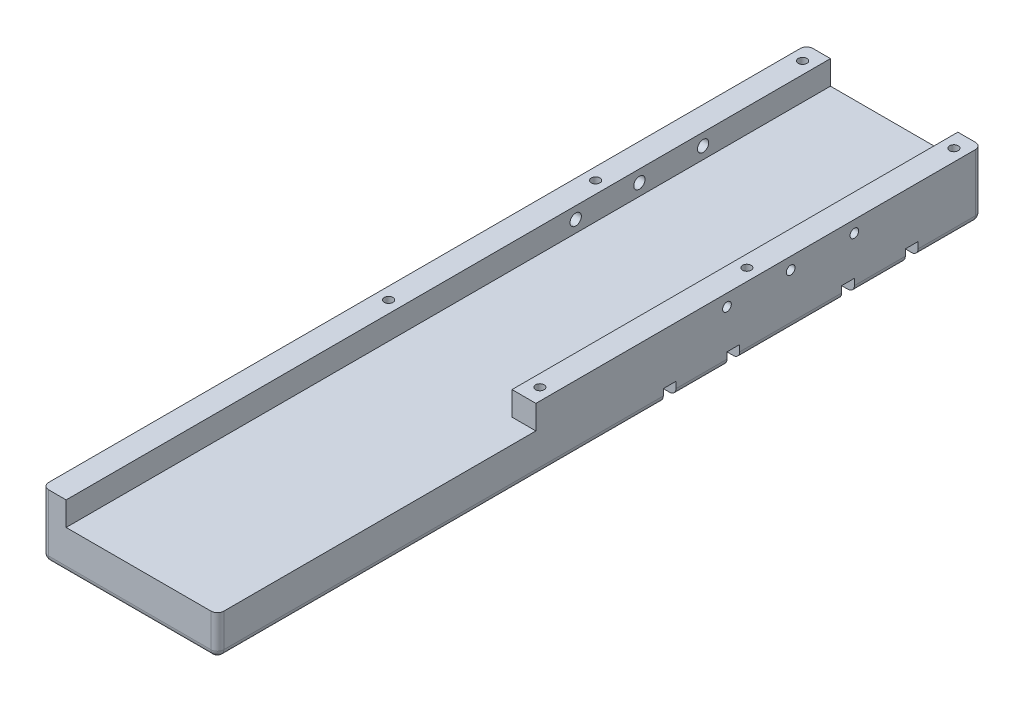
SolidWorks part; units mm, degrees
ref_plane "Front Plane" through (0, 0, 0) normal (0, 0, 1) x (1, 0, 0)
ref_plane "Top Plane" through (0, 0, 0) normal (0, 1, 0) x (1, 0, 0)
ref_plane "Right Plane" through (0, 0, 0) normal (1, 0, 0) x (0, 0, -1)
sketch "Sketch1" plane through (0, 0, 0) normal (0, 1, 0) x (1, 0, 0)
  line L1 (0, 0) -> (69.85, 0)
  line L2 (0, 0) -> (0, 304.8)
  line L3 (0, 304.8) -> (69.85, 304.8)
  line L4 (69.85, 0) -> (69.85, 304.8)
  dimension "D1" = 69.85
  dimension "D2" = 304.8
extrude "Boss-Extrude1" add sketch "Sketch1" along normal blind 25.4
fillet "Fillet1" radius 2.54 8 edges at (69.85, 12.7, -304.8) (0, 12.7, -304.8) (34.925, 0, -304.8) (0, 12.7, 0) (69.85, 12.7, 0) (34.925, 0, 0) (69.85, 0, -152.4) (0, 0, -152.4)
sketch "Sketch2" plane through (0, 0, 0) normal (0, -1, 0) x (1, 0, 0)
  line L0 (69.85, 0) -> (69.85, -304.8) construction
  line L1 (69.85, -177.8) -> (0, -177.8)
  line L2 (69.85, -177.8) -> (69.85, -182.88)
  line L3 (69.85, -182.88) -> (0, -182.88)
  line L4 (0, -177.8) -> (0, -182.88)
  line L5 (0, -304.8) -> (0, 0) construction
  line L7 (69.85, -203.2) -> (0, -203.2)
  line L8 (69.85, -203.2) -> (69.85, -208.28)
  line L9 (69.85, -208.28) -> (0, -208.28)
  line L10 (0, -203.2) -> (0, -208.28)
  line L11 (69.85, -248.92) -> (0, -248.92)
  line L12 (69.85, -248.92) -> (69.85, -254)
  line L13 (69.85, -254) -> (0, -254)
  line L14 (0, -248.92) -> (0, -254)
  line L15 (69.85, -274.32) -> (0, -274.32)
  line L16 (69.85, -274.32) -> (69.85, -279.4)
  line L17 (69.85, -279.4) -> (0, -279.4)
  line L18 (0, -274.32) -> (0, -279.4)
  line L19 (69.85, -304.8) -> (0, -304.8) construction
  dimension "D1" = 5.08
  dimension "D2" = 25.4
  dimension "D3" = 45.72
  dimension "D5" = 25.4
  dimension "D4" = 2
extrude "Cut-Extrude1" cut sketch "Sketch2" against normal blind 5.08
sketch "Sketch3" plane through (0, 25.4, 0) normal (0, 1, 0) x (1, 0, 0)
  line L0 (67.31, 304.8) -> (2.54, 304.8) construction
  line L1 (9.525, 304.8) -> (60.325, 304.8)
  line L2 (9.525, 304.8) -> (9.525, 0)
  line L3 (9.525, 0) -> (60.325, 0)
  line L4 (60.325, 304.8) -> (60.325, 0)
  line L5 (2.54, 0) -> (67.31, 0) construction
  line L6 (0, 302.26) -> (0, 2.54) construction
  line L7 (69.85, 2.54) -> (69.85, 302.26) construction
  dimension "D1" = 9.525
  dimension "D2" = 9.525
extrude "Cut-Extrude2" cut sketch "Sketch3" against normal blind 9.525
sketch "Sketch4" plane through (0, 0, 0) normal (-1, 0, 0) x (0, 0, 1)
  line L0 (-304.8, 20.6375) -> (0, 20.6375) construction
  line L1 (-304.8, 2.54) -> (-304.8, 25.4) construction
  line L3 (-302.26, 25.4) -> (-2.54, 25.4) construction
  line L4 (0, 25.4) -> (0, 2.54) construction
  circle A0 centre (-203.2, 20.6375) radius 2.2479
  circle A1 centre (-228.6, 20.6375) radius 2.2479
  circle A2 centre (-254, 20.6375) radius 2.2479
  dimension "D2" = 50.8
  dimension "D3" = 25.4
  dimension "D4" = 25.4
  dimension "D5" = 4.4958
  dimension "D1" = 4.7625
extrude "Cut-Extrude3" cut sketch "Sketch4" against normal up to next
hole_wizard "#8-32 Tapped Hole1" positions "Sketch10" profile "Sketch11" tap size "#8-32" standard "ANSI Inch"
sketch "Sketch10" plane through (0, 25.4, 0) normal (0, 1, 0) x (1, 0, 0)
  line L0 (67.31, 304.8) -> (60.325, 304.8) construction
  line L1 (69.85, 2.54) -> (69.85, 302.26) construction
  line L3 (69.85, 215.9) -> (-11.011, 215.9) construction
  line L5 (0, 302.26) -> (0, 2.54) construction
  point P0 (65.0875, 298.45)
  point P3 (4.7625, 298.45)
  point P6 (65.0875, 215.9)
  point P9 (4.7625, 215.9)
  point P44 (65.0875, 133.35)
  point P45 (4.7625, 133.35)
  point P47 (4.7625, 215.9)
  dimension "D1" = 6.35
  dimension "D2" = 4.7625
  dimension "D3" = 82.55
  dimension "D4" = 4.7625
sketch "Sketch11" plane through (65.0875, 25.4, -298.45) normal (1, 0, 0) x (0, 0, 1)
  line L0 (0, 0) -> (0, 11.7058)
  line L1 (0, 11.7058) -> (1.7272, 10.668)
  line L2 (1.7272, 10.668) -> (1.7272, 0)
  line L5 (1.7272, 0) -> (0, 0)
  line L10 (0, 11.7058) -> (-1.7272, 10.668) construction
  line L11 (0, -6.35) -> (0, 107.95) construction
  dimension "Tap Drill Dia." = 3.4544
  dimension "Tap Drill Depth" = 10.668
  dimension "Drill Angle" = 118
cosmetic thread "Hole Thread1" parameters "D1"=8.382, "D2"=4.1656
cosmetic thread "Hole Thread2" parameters "D1"=8.382, "D2"=4.1656
cosmetic thread "Hole Thread3" parameters "D1"=8.382, "D2"=4.1656
cosmetic thread "Hole Thread4" parameters "D1"=8.382, "D2"=4.1656
cosmetic thread "Hole Thread7" parameters "D1"=8.382, "D2"=4.1656
cosmetic thread "Hole Thread8" parameters "D1"=8.382, "D2"=4.1656
cosmetic thread "Hole Thread25" parameters "D1"=8.382, "D2"=4.1656
hole_wizard "#8-32 Tapped Hole2" positions "Sketch12" profile "Sketch13" tap size "#8-32" standard "ANSI Inch" end condition up to next
sketch "Sketch12" plane through (69.85, 0, 0) normal (1, 0, 0) x (0, 0, -1)
  line L0 (2.54, 25.4) -> (302.26, 25.4) construction
  line L2 (304.8, 25.4) -> (304.8, 2.54) construction
  point P0 (203.2, 20.6375)
  point P2 (228.6, 20.6375)
  point P4 (254, 20.6375)
  dimension "D1" = 4.7625
  dimension "D2" = 25.4
  dimension "D3" = 25.4
  dimension "D4" = 50.8
sketch "Sketch13" plane through (69.85, 20.6375, -203.2) normal (0, 1, 0) x (0, 0, -1)
  line L0 (0, 0) -> (0, 9.525)
  line L1 (0, 9.525) -> (1.7272, 9.525)
  line L2 (1.7272, 9.525) -> (1.7272, 0)
  line L5 (1.7272, 0) -> (0, 0)
  line L11 (0, -6.35) -> (0, 107.95) construction
  dimension "Thru Tap Drill Dia." = 3.4544
  dimension "Thru Tap Drill Depth" = 9.525
cosmetic thread "Hole Thread9" parameters "D2"=4.1656
cosmetic thread "Hole Thread10" parameters "D2"=4.1656
cosmetic thread "Hole Thread11" parameters "D2"=4.1656
hole_wizard "#8-32 Tapped Hole3" positions "Sketch14" profile "Sketch15" tap size "#8-32" standard "ANSI Inch"
sketch "Sketch14" plane through (0, 0, 0) normal (0, -1, 0) x (-1, 0, 0)
  line L0 (0, 302.26) -> (0, 279.4) construction
  line L1 (-69.85, 279.4) -> (-69.85, 302.26) construction
  line L2 (-2.54, 264.16) -> (-65.2153, 264.16) construction
  line L3 (-2.54, 254) -> (-2.54, 274.32) construction
  line L5 (-2.54, 193.04) -> (-66.4882, 193.04) construction
  line L6 (-2.54, 182.88) -> (-2.54, 203.2) construction
  line L8 (-2.54, 279.4) -> (-67.31, 279.4) construction
  line L9 (-67.31, 248.92) -> (-2.54, 248.92) construction
  line L10 (-2.54, 208.28) -> (-67.31, 208.28) construction
  line L11 (-67.31, 177.8) -> (-2.54, 177.8) construction
  point P0 (-12.7, 289.56)
  point P2 (-57.15, 289.56)
  point P4 (-12.7, 264.16)
  point P6 (-57.15, 264.16)
  point P8 (-12.7, 238.76)
  point P10 (-57.15, 238.76)
  point P12 (-12.7, 218.44)
  point P14 (-57.15, 218.44)
  point P16 (-12.7, 193.04)
  point P18 (-57.15, 193.04)
  point P20 (-12.7, 167.64)
  point P22 (-57.15, 167.64)
  dimension "D1" = 12.7
  dimension "D2" = 12.7
  dimension "D3" = 10.16
  dimension "D4" = 10.16
  dimension "D5" = 10.16
  dimension "D6" = 10.16
cosmetic thread "Hole Thread12" parameters "D1"=8.382, "D2"=4.1656
cosmetic thread "Hole Thread13" parameters "D1"=8.382, "D2"=4.1656
cosmetic thread "Hole Thread14" parameters "D1"=8.382, "D2"=4.1656
cosmetic thread "Hole Thread15" parameters "D1"=8.382, "D2"=4.1656
cosmetic thread "Hole Thread16" parameters "D1"=8.382, "D2"=4.1656
cosmetic thread "Hole Thread17" parameters "D1"=8.382, "D2"=4.1656
cosmetic thread "Hole Thread18" parameters "D1"=8.382, "D2"=4.1656
cosmetic thread "Hole Thread19" parameters "D1"=8.382, "D2"=4.1656
cosmetic thread "Hole Thread20" parameters "D1"=8.382, "D2"=4.1656
cosmetic thread "Hole Thread21" parameters "D1"=8.382, "D2"=4.1656
cosmetic thread "Hole Thread22" parameters "D1"=8.382, "D2"=4.1656
cosmetic thread "Hole Thread23" parameters "D1"=8.382, "D2"=4.1656
sketch "Sketch15" plane through (12.7, 0, -289.56) normal (1, 0, 0) x (0, 0, -1)
  line L0 (0, 0) -> (0, 13.7378)
  line L1 (0, 13.7378) -> (1.7272, 12.7)
  line L2 (1.7272, 12.7) -> (1.7272, 0)
  line L5 (1.7272, 0) -> (0, 0)
  line L10 (0, 13.7378) -> (-1.7272, 12.7) construction
  line L11 (0, -6.35) -> (0, 107.95) construction
  dimension "Tap Drill Dia." = 3.4544
  dimension "Tap Drill Depth" = 12.7
  dimension "Drill Angle" = 118
sketch "Sketch16" plane through (0, 0, 0) normal (0, 0, 1) x (1, 0, 0)
  line L0 (69.85, 25.4) -> (69.85, 2.54) construction
  line L1 (60.325, 15.875) -> (69.85, 15.875)
  line L2 (60.325, 15.875) -> (60.325, 25.4)
  line L3 (60.325, 25.4) -> (69.85, 25.4)
  line L4 (69.85, 15.875) -> (69.85, 25.4)
  line L5 (60.325, 25.4) -> (67.31, 25.4) construction
extrude "Cut-Extrude4" cut sketch "Sketch16" against normal blind 127
